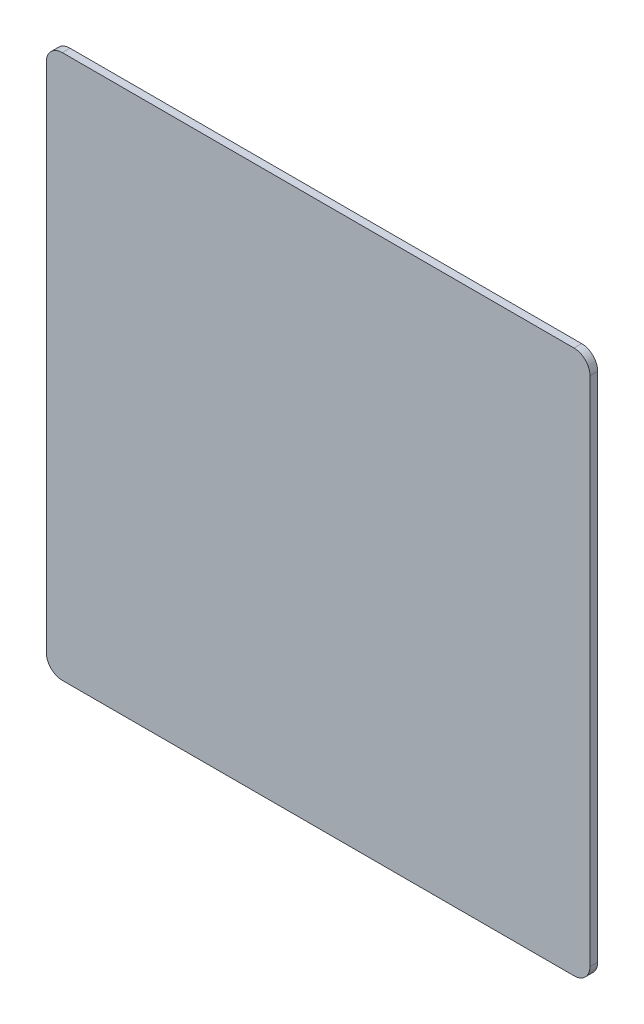
SolidWorks part; units mm, degrees
ref_plane "Ön Düzlem" through (0, 0, 0) normal (0, 0, 1) x (1, 0, 0)
ref_plane "Üst Düzlem" through (0, 0, 0) normal (0, 1, 0) x (1, 0, 0)
ref_plane "Sağ Düzlem" through (0, 0, 0) normal (1, 0, 0) x (0, 0, -1)
ref_plane "Plane1" through (0, 0, 0.12) normal (0, 0, 1) x (1, 0, 0)
sketch "Sketch1" plane through (0, 0, 0.12) normal (0, 0, 1) x (1, 0, 0)
  line L0 (8.25, 0.25) -> (8.25, 8.25)
  line L1 (8, 8.5) -> (0, 8.5)
  line L2 (-0.25, 8.25) -> (-0.25, 0.25)
  line L11 (0, 0) -> (8, 0)
  arc A0 (8, 0) -> (8.25, 0.25) centre (8, 0.25) ccw
  arc A1 (8.25, 8.25) -> (8, 8.5) centre (8, 8.25) ccw
  arc A2 (0, 8.5) -> (-0.25, 8.25) centre (0, 8.25) ccw
  arc A3 (-0.25, 0.25) -> (0, 0) centre (0, 0.25) ccw
  point P11 (-0.5705, 1.3539)
  point P13 (0, 0)
  point P14 (0, 0)
  point P15 (-6.8176, 7.3552)
  point P16 (0, 0)
  dimension "D3" = 0.25
  dimension "D1" = 8.5
  dimension "D2" = 8.5
extrude "Boss-Extrude1" add sketch "Sketch1" against normal blind 0.12
